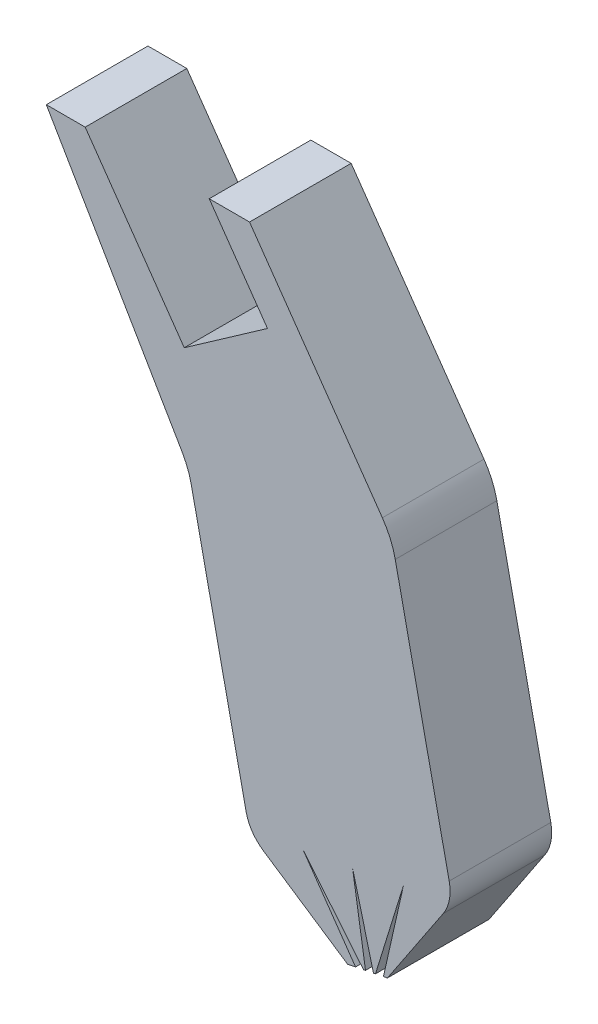
SolidWorks part; units mm, degrees
ref_plane "Front Plane" through (0, 0, 0) normal (0, 0, 1) x (1, 0, 0)
ref_plane "Top Plane" through (0, 0, 0) normal (0, 1, 0) x (1, 0, 0)
ref_plane "Right Plane" through (0, 0, 0) normal (1, 0, 0) x (0, 0, -1)
sketch "Sketch6" plane through (0, 0, 0) normal (0, 0, 1) x (1, 0, 0)
  line L0 (0, 0) -> (-50, 0)
  line L1 (-50, 0) -> (-15, -60)
  line L2 (-15, -60) -> (0, -130)
  line L3 (0, -130) -> (30, -150)
  line L4 (30, -150) -> (50, -120)
  line L5 (50, -120) -> (35, -50)
  line L6 (35, -50) -> (0, 0)
  dimension "D1" = 50
  dimension "D2" = 60
  dimension "D3" = 130
  dimension "D4" = 150
  dimension "D5" = 85
  dimension "D6" = 100
  dimension "D7" = 30
  dimension "D8" = 15
extrude "Main Extrude" add sketch "Sketch6" along normal blind 25
sketch "Sketch9" plane through (0, 0, 0) normal (0, 0, -1) x (-1, 0, 0)
  line L0 (-30, -150) -> (-24.1165, -146.0777)
  line L1 (0, -130) -> (-30, -150) construction
  line L2 (-24.1165, -146.0777) -> (-33.9223, -144.1165)
  line L3 (-30, -150) -> (-50, -120) construction
  line L4 (-33.9223, -144.1165) -> (-30, -150)
  dimension "D1" = 7.0711
  dimension "D2" = 7.0711
extrude "Bottom Foot Cut" cut sketch "Sketch9" against normal through all
sketch "Sketch11" plane through (0, 0, 0) normal (0, 0, -1) x (-1, 0, 0)
  line L2 (-26.0777, -145.6854) -> (-28.0388, -145.2932)
  line L4 (-30.9806, -144.7049) -> (-32.9417, -144.3126)
  line L5 (-13.2927, -127.3415) -> (-26.0777, -145.6854)
  line L6 (-26.0777, -145.6854) -> (-28.0388, -145.2932)
  line L7 (-28.0388, -145.2932) -> (-13.2927, -127.3415)
  line L8 (-25.3423, -124.9315) -> (-28.5291, -145.1952)
  line L9 (-28.5291, -145.1952) -> (-30.4903, -144.8029)
  line L10 (-30.4903, -144.8029) -> (-25.3423, -124.9315)
  line L11 (-28.5291, -145.1952) -> (-30.4903, -144.8029)
  line L12 (-37.8697, -122.4261) -> (-32.9417, -144.3126)
  line L13 (-32.9417, -144.3126) -> (-30.9806, -144.7049)
  line L14 (-30.9806, -144.7049) -> (-37.8697, -122.4261)
  line M1 (-33.9223, -144.1165) -> (-24.1165, -146.0777)
  dimension "D1" = 2
  dimension "D2" = 2
  dimension "D3" = 2
  dimension "D4" = 4.5
  dimension "D5" = 2
  dimension "D6" = 7
extrude "Talon Cuts" cut sketch "Sketch11" against normal through all contours L14 L12 M1 | L10 L8 M1 | L7 L5 M1
fillet "Ankle Fillets" radius 10 2 edges at (0, -130, 12.5) (50, -120, 12.5)
fillet "Inner Leg Fillet" radius 20 1 edges at (-15, -60, 12.5)
fillet "Knee Fillet" radius 20 1 edges at (35, -50, 12.5)
scale "Scale1" scale about centroid uniform scaling yes scale factor 0.1
sketch "Sketch12" plane through (0, 0, 11.25) normal (0, 0, -1) x (-1, 0, 0)
  line L0 (-7.0126, -61.1492) -> (-2.0126, -61.1492) construction
  line L2 (-7.0126, -61.1492) -> (-8.1201, -62.7314) construction
  line L4 (-10.2803, -65.8174) -> (-7.0126, -61.1492) construction
  line L5 (-6.0208, -61.1492) -> (-7.4544, -63.1973) construction
  line L6 (-6.0208, -61.1492) -> (-7.4544, -63.1973)
  line L11 (-7.4544, -63.1973) -> (-5.4064, -64.631)
  line L12 (-7.4544, -63.1973) -> (-8.1201, -62.7314) construction
  line L13 (-5.4064, -64.631) -> (-2.9691, -61.1492)
  line L14 (-6.0208, -61.1492) -> (-2.9691, -61.1492)
  dimension "D1" = 0.8125
extrude "Cut-Extrude3" cut sketch "Sketch12" against normal up to next
